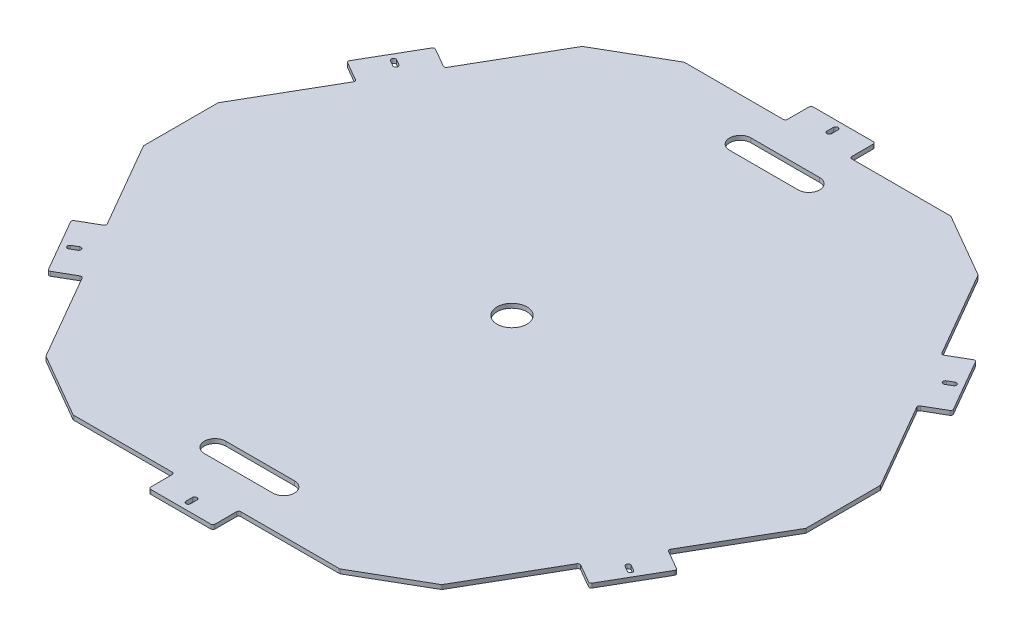
SolidWorks part; units mm, degrees
material "PE High Density"
ref_plane "Front Plane" through (0, 0, 0) normal (0, 0, 1) x (1, 0, 0)
ref_plane "Top Plane" through (0, 0, 0) normal (0, 1, 0) x (1, 0, 0)
ref_plane "Right Plane" through (0, 0, 0) normal (1, 0, 0) x (0, 0, -1)
sketch "Sketch1" plane through (0, 0, 0) normal (0, 1, 0) x (1, 0, 0)
  line L155 (359.0984, -359.0984) -> (490.5375, -131.4391)
  line L173 (490.5375, -131.4391) -> (490.5375, 131.4391)
  line L176 (490.5375, 131.4391) -> (359.0984, 359.0984)
  line L197 (359.0984, 359.0984) -> (131.4391, 490.5375)
  line L198 (131.4391, 490.5375) -> (-131.4391, 490.5375)
  line L201 (-131.4391, 490.5375) -> (-359.0984, 359.0984)
  line L204 (-359.0984, 359.0984) -> (-490.5375, 131.4391)
  line L207 (-490.5375, 131.4391) -> (-490.5375, -131.4391)
  line L210 (-490.5375, -131.4391) -> (-359.0984, -359.0984)
  line L211 (-359.0984, -359.0984) -> (-131.4391, -490.5375)
  line L212 (-131.4391, -490.5375) -> (131.4391, -490.5375)
  line L213 (131.4391, -490.5375) -> (359.0984, -359.0984)
  circle A42 centre (0, 0) radius 490.5375 construction
  dimension "D1" = 981.075
extrude "Boss-Extrude1" add sketch "Sketch1" along normal blind 6.35
sketch "Sketch2" plane through (0, 6.35, 0) normal (0, 1, 0) x (1, 0, 0)
  line L0 (-131.4391, 490.5375) -> (-197.4303, 452.4375)
  line L1 (-131.4391, 490.5375) -> (-359.0984, 359.0984) construction
  line L2 (-197.4303, 452.4375) -> (-47.625, 452.4375)
  line L3 (-47.625, 452.4375) -> (-47.625, 490.5375)
  line L4 (131.4391, 490.5375) -> (-131.4391, 490.5375) construction
  line L5 (-47.625, 490.5375) -> (-131.4391, 490.5375)
  line L6 (131.4391, 490.5375) -> (47.625, 490.5375)
  line L7 (47.625, 490.5375) -> (47.625, 452.4375)
  line L8 (47.625, 452.4375) -> (197.4303, 452.4375)
  line L9 (359.0984, 359.0984) -> (131.4391, 490.5375) construction
  line L10 (197.4303, 452.4375) -> (131.4391, 490.5375)
  line L11 (0, 479.425) -> (0, 469.9) construction
  line L12 (3.3734, 479.425) -> (3.3734, 469.9)
  line L13 (-3.3734, 479.425) -> (-3.3734, 469.9)
  line L14 (-50.8, 388.9375) -> (50.8, 388.9375) construction
  line L15 (-50.8, 404.8125) -> (50.8, 404.8125)
  line L16 (-50.8, 373.0625) -> (50.8, 373.0625)
  line L17 (401.0054, 286.5132) -> (359.0984, 359.0984)
  line L18 (359.0984, 359.0984) -> (293.1072, 397.1984)
  line L19 (293.1072, 397.1984) -> (368.0099, 267.4632)
  line L20 (368.0099, 267.4632) -> (401.0054, 286.5132)
  line L21 (490.5375, 55.2391) -> (490.5375, 131.4391)
  line L22 (490.5375, 131.4391) -> (448.6304, 204.0243)
  line L23 (448.6304, 204.0243) -> (415.6349, 184.9743)
  line L24 (415.6349, 184.9743) -> (490.5375, 55.2391)
  line L25 (448.6304, -204.0243) -> (490.5375, -131.4391)
  line L26 (490.5375, -131.4391) -> (490.5375, -55.2391)
  line L27 (490.5375, -55.2391) -> (415.6349, -184.9743)
  line L28 (415.6349, -184.9743) -> (448.6304, -204.0243)
  line L29 (293.1072, -397.1984) -> (359.0984, -359.0984)
  line L30 (359.0984, -359.0984) -> (401.0054, -286.5132)
  line L31 (401.0054, -286.5132) -> (368.0099, -267.4632)
  line L32 (368.0099, -267.4632) -> (293.1072, -397.1984)
  line L33 (47.625, -490.5375) -> (131.4391, -490.5375)
  line L34 (131.4391, -490.5375) -> (197.4303, -452.4375)
  line L35 (197.4303, -452.4375) -> (47.625, -452.4375)
  line L36 (47.625, -452.4375) -> (47.625, -490.5375)
  line L37 (-197.4303, -452.4375) -> (-131.4391, -490.5375)
  line L38 (-131.4391, -490.5375) -> (-47.625, -490.5375)
  line L39 (-47.625, -490.5375) -> (-47.625, -452.4375)
  line L40 (-47.625, -452.4375) -> (-197.4303, -452.4375)
  line L41 (-401.0054, -286.5132) -> (-359.0984, -359.0984)
  line L42 (-359.0984, -359.0984) -> (-293.1072, -397.1984)
  line L43 (-293.1072, -397.1984) -> (-368.0099, -267.4632)
  line L44 (-368.0099, -267.4632) -> (-401.0054, -286.5132)
  line L45 (-490.5375, -55.2391) -> (-490.5375, -131.4391)
  line L46 (-490.5375, -131.4391) -> (-448.6304, -204.0243)
  line L47 (-448.6304, -204.0243) -> (-415.6349, -184.9743)
  line L48 (-415.6349, -184.9743) -> (-490.5375, -55.2391)
  line L49 (-448.6304, 204.0243) -> (-490.5375, 131.4391)
  line L50 (-490.5375, 131.4391) -> (-490.5375, 55.2391)
  line L51 (-490.5375, 55.2391) -> (-415.6349, 184.9743)
  line L52 (-415.6349, 184.9743) -> (-448.6304, 204.0243)
  line L53 (-293.1072, 397.1984) -> (-359.0984, 359.0984)
  line L54 (-359.0984, 359.0984) -> (-401.0054, 286.5132)
  line L55 (-401.0054, 286.5132) -> (-368.0099, 267.4632)
  line L56 (-368.0099, 267.4632) -> (-293.1072, 397.1984)
  line L57 (-359.0984, 359.0984) -> (-490.5375, 131.4391) construction
  line L58 (-490.5375, 0) -> (490.5375, 0) construction
  line L59 (-490.5375, 131.4391) -> (-490.5375, -131.4391) construction
  line L60 (490.5375, -131.4391) -> (490.5375, 131.4391) construction
  line L61 (-415.1942, 239.7125) -> (-406.9453, 234.95) construction
  line L62 (-413.5075, 242.634) -> (-405.2586, 237.8715)
  line L63 (-416.8809, 236.791) -> (-408.6321, 232.0285)
  line L64 (415.1942, 239.7125) -> (406.9453, 234.95) construction
  line L65 (416.8809, 236.791) -> (408.6321, 232.0285)
  line L66 (413.5075, 242.634) -> (405.2586, 237.8715)
  line L67 (490.5375, 131.4391) -> (359.0984, 359.0984) construction
  line L68 (415.1942, -239.7125) -> (406.9453, -234.95) construction
  line L69 (416.8809, -236.791) -> (408.6321, -232.0285)
  line L70 (413.5075, -242.634) -> (405.2586, -237.8715)
  line L71 (-50.8, -388.9375) -> (50.8, -388.9375) construction
  line L72 (-50.8, -404.8125) -> (50.8, -404.8125)
  line L73 (-50.8, -373.0625) -> (50.8, -373.0625)
  line L74 (0, -479.425) -> (0, -469.9) construction
  line L75 (3.3734, -479.425) -> (3.3734, -469.9)
  line L76 (-3.3734, -479.425) -> (-3.3734, -469.9)
  line L77 (-415.1942, -239.7125) -> (-406.9453, -234.95) construction
  line L78 (-413.5075, -242.634) -> (-405.2586, -237.8715)
  line L79 (-416.8809, -236.791) -> (-408.6321, -232.0285)
  arc A0 (3.3734, 479.425) -> (-3.3734, 479.425) centre (0, 479.425) ccw
  arc A1 (-3.3734, 469.9) -> (3.3734, 469.9) centre (0, 469.9) ccw
  arc A2 (-50.8, 404.8125) -> (-50.8, 373.0625) centre (-50.8, 388.9375) ccw
  arc A3 (50.8, 373.0625) -> (50.8, 404.8125) centre (50.8, 388.9375) ccw
  arc A4 (-413.5075, 242.634) -> (-416.8809, 236.791) centre (-415.1942, 239.7125) ccw
  arc A5 (-408.6321, 232.0285) -> (-405.2586, 237.8715) centre (-406.9453, 234.95) ccw
  arc A6 (416.8809, 236.791) -> (413.5075, 242.634) centre (415.1942, 239.7125) ccw
  arc A7 (405.2586, 237.8715) -> (408.6321, 232.0285) centre (406.9453, 234.95) ccw
  arc A8 (416.8809, -236.791) -> (413.5075, -242.634) centre (415.1942, -239.7125) cw
  arc A9 (405.2586, -237.8715) -> (408.6321, -232.0285) centre (406.9453, -234.95) cw
  arc A10 (-50.8, -404.8125) -> (-50.8, -373.0625) centre (-50.8, -388.9375) cw
  arc A11 (50.8, -373.0625) -> (50.8, -404.8125) centre (50.8, -388.9375) cw
  arc A12 (3.3734, -479.425) -> (-3.3734, -479.425) centre (0, -479.425) cw
  arc A13 (-3.3734, -469.9) -> (3.3734, -469.9) centre (0, -469.9) cw
  arc A14 (-413.5075, -242.634) -> (-416.8809, -236.791) centre (-415.1942, -239.7125) cw
  arc A15 (-408.6321, -232.0285) -> (-405.2586, -237.8715) centre (-406.9453, -234.95) cw
  circle A16 centre (0, 0) radius 22.225
  point P18 (0, 474.6625)
  point P26 (0, 388.9375)
  point P32 (0, 490.5375)
  point P75 (0, 0)
  point P83 (-411.0698, 237.3313)
  point P90 (411.0698, 237.3313)
  point P99 (411.0698, -237.3313)
  point P106 (0, -388.9375)
  point P113 (0, -474.6625)
  point P120 (-411.0698, -237.3313)
  dimension "D4" = 3.3734
  dimension "D14" = 44.45
  dimension "D1" = 95.25
  dimension "D2" = 38.1
  dimension "D3" = 9.525
  dimension "D5" = 15.875
  dimension "D6" = 31.75
  dimension "D7" = 101.6
  dimension "D8" = 101.6
  dimension "D10" = 47.625
  dimension "D11" = 15.875
  dimension "D12" = 15.875
  dimension "D13" = 47.625
  dimension "D9" = 6
extrude "Cut-Extrude1" cut sketch "Sketch2" against normal blind 6.35
fillet "Fillet2" radius 3.175 36 edges at (-47.625, 3.175, 490.5375) (47.625, 3.175, 490.5375) (47.625, 3.175, 452.4375) (197.4303, 3.175, 452.4375) (293.1072, 3.175, 397.1984) (368.0099, 3.175, 267.4632) (401.0054, 3.175, 286.5132) (448.6304, 3.175, 204.0243) (415.6349, 3.175, 184.9743) (490.5375, 3.175, 55.2391) (490.5375, 3.175, -55.2391) (415.6349, 3.175, -184.9743) (448.6304, 3.175, -204.0243) (401.0054, 3.175, -286.5132) (368.0099, 3.175, -267.4632) (293.1072, 3.175, -397.1984) (197.4303, 3.175, -452.4375) (47.625, 3.175, -452.4375) (47.625, 3.175, -490.5375) (-47.625, 3.175, -490.5375) (-47.625, 3.175, -452.4375) (-197.4303, 3.175, -452.4375) (-368.0099, 3.175, -267.4632) (-401.0054, 3.175, -286.5132) (-448.6304, 3.175, -204.0243) (-415.6349, 3.175, -184.9743) (-490.5375, 3.175, -55.2391) (-490.5375, 3.175, 55.2391) (-415.6349, 3.175, 184.9743) (-448.6304, 3.175, 204.0243) (-401.0054, 3.175, 286.5132) (-368.0099, 3.175, 267.4632) (-293.1072, 3.175, 397.1984) (-197.4303, 3.175, 452.4375) (-47.625, 3.175, 452.4375) (-293.1072, 3.175, -397.1984)
